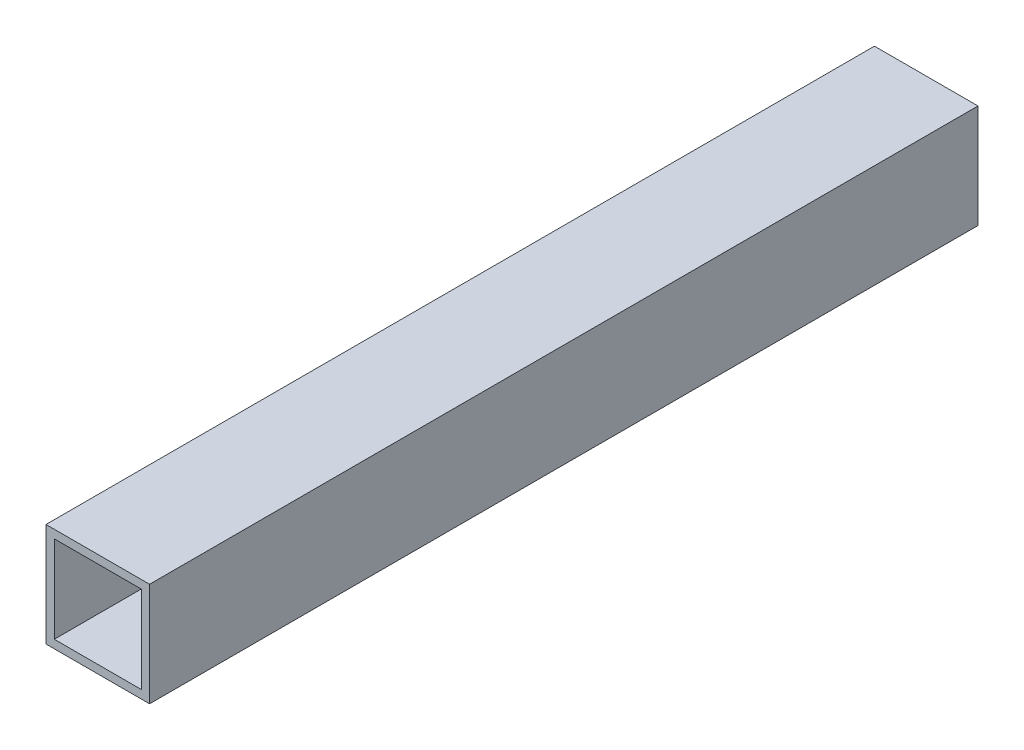
SolidWorks part; units mm, degrees
ref_plane "Front Plane" through (0, 0, 0) normal (0, 0, 1) x (1, 0, 0)
ref_plane "Top Plane" through (0, 0, 0) normal (0, 1, 0) x (1, 0, 0)
ref_plane "Right Plane" through (0, 0, 0) normal (1, 0, 0) x (0, 0, -1)
sketch "Sketch2" plane through (0, 0, 0) normal (0, 0, 1) x (1, 0, 0)
  line L1 (-19.05, 19.05) -> (19.05, 19.05)
  line L2 (-19.05, 19.05) -> (-19.05, -19.05)
  line L3 (-19.05, -19.05) -> (19.05, -19.05)
  line L4 (19.05, 19.05) -> (19.05, -19.05)
  line L5 (-19.05, 19.05) -> (19.05, -19.05) construction
  line L6 (-19.05, -19.05) -> (19.05, 19.05) construction
  line L11 (-16.002, -16.002) -> (16.002, -16.002)
  line L12 (-16.002, -16.002) -> (-16.002, 16.002)
  line L13 (-16.002, 16.002) -> (16.002, 16.002)
  line L14 (16.002, -16.002) -> (16.002, 16.002)
  line L15 (-16.002, -16.002) -> (16.002, 16.002) construction
  line L16 (-16.002, 16.002) -> (16.002, -16.002) construction
  point P0 (0, 0)
  point P6 (0, 0)
  dimension "D1" = 38.1
  dimension "D2" = 3.048
extrude "Boss-Extrude1" add sketch "Sketch2" along normal blind 304.8
